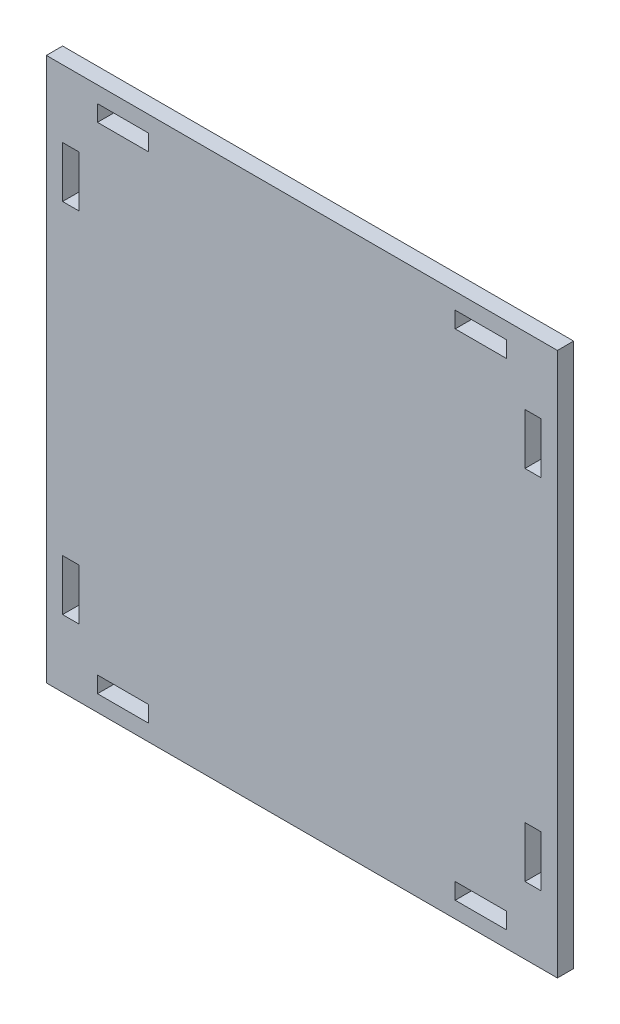
SolidWorks part; units mm, degrees
ref_plane "Front Plane" through (0, 0, 0) normal (0, 0, 1) x (1, 0, 0)
ref_plane "Top Plane" through (0, 0, 0) normal (0, 1, 0) x (1, 0, 0)
ref_plane "Right Plane" through (0, 0, 0) normal (1, 0, 0) x (0, 0, -1)
sketch "Sketch1" plane through (0, 0, 0) normal (0, 0, 1) x (1, 0, 0)
  line L0 (50, 106.35) -> (50, 41.5962) construction
  line L1 (0, 0) -> (100, 0)
  line L2 (0, 0) -> (0, 106.35)
  line L3 (0, 106.35) -> (100, 106.35)
  line L4 (100, 0) -> (100, 106.35)
  line L5 (3.175, 83.175) -> (6.35, 83.175)
  line L6 (3.175, 83.175) -> (3.175, 93.175)
  line L7 (3.175, 93.175) -> (6.35, 93.175)
  line L8 (6.35, 83.175) -> (6.35, 93.175)
  line L9 (10, 103.175) -> (20, 103.175)
  line L10 (10, 103.175) -> (10, 100)
  line L11 (10, 100) -> (20, 100)
  line L12 (20, 103.175) -> (20, 100)
  line L13 (80, 103.175) -> (80, 100)
  line L14 (90, 100) -> (80, 100)
  line L15 (90, 103.175) -> (90, 100)
  line L16 (90, 103.175) -> (80, 103.175)
  line L17 (93.65, 83.175) -> (93.65, 93.175)
  line L18 (96.825, 93.175) -> (93.65, 93.175)
  line L19 (96.825, 83.175) -> (96.825, 93.175)
  line L20 (96.825, 83.175) -> (93.65, 83.175)
  line L21 (0, 53.175) -> (72.9598, 53.175) construction
  line L22 (96.825, 23.175) -> (93.65, 23.175)
  line L23 (96.825, 23.175) -> (96.825, 13.175)
  line L24 (96.825, 13.175) -> (93.65, 13.175)
  line L25 (93.65, 23.175) -> (93.65, 13.175)
  line L26 (90, 3.175) -> (80, 3.175)
  line L27 (90, 3.175) -> (90, 6.35)
  line L28 (90, 6.35) -> (80, 6.35)
  line L29 (80, 3.175) -> (80, 6.35)
  line L30 (20, 3.175) -> (20, 6.35)
  line L31 (10, 6.35) -> (20, 6.35)
  line L32 (10, 3.175) -> (10, 6.35)
  line L33 (10, 3.175) -> (20, 3.175)
  line L34 (6.35, 23.175) -> (6.35, 13.175)
  line L35 (3.175, 13.175) -> (6.35, 13.175)
  line L36 (3.175, 23.175) -> (3.175, 13.175)
  line L37 (3.175, 23.175) -> (6.35, 23.175)
  dimension "D1" = 100
  dimension "D2" = 106.35
  dimension "D3" = 3.175
  dimension "D4" = 13.175
  dimension "D5" = 3.175
  dimension "D6" = 10
  dimension "D7" = 10
  dimension "D8" = 3.175
  dimension "D9" = 3.175
  dimension "D10" = 10
extrude "Boss-Extrude1" add sketch "Sketch1" along normal blind 3.175
